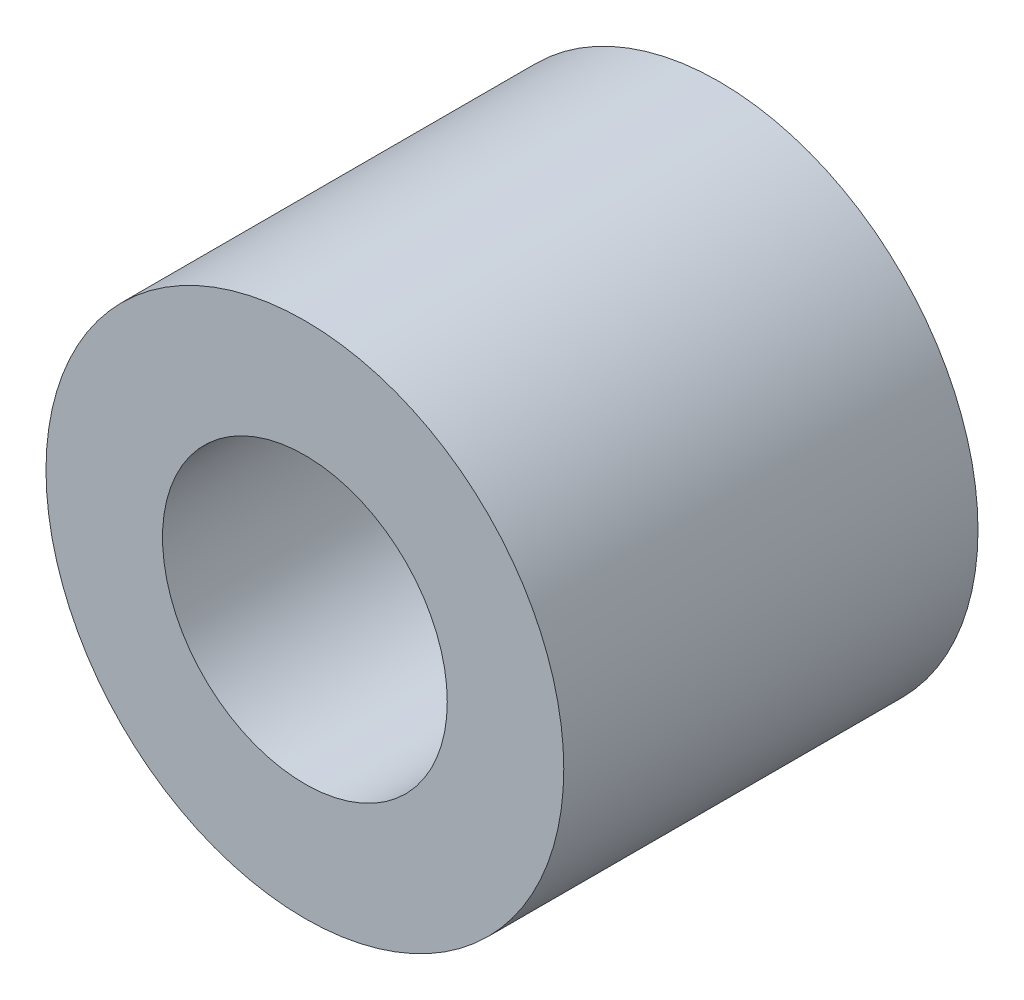
SolidWorks part; units mm, degrees
ref_plane "Plano frontal" through (0, 0, 0) normal (0, 0, 1) x (1, 0, 0)
ref_plane "Plano superior" through (0, 0, 0) normal (0, 1, 0) x (1, 0, 0)
ref_plane "Plano direito" through (0, 0, 0) normal (1, 0, 0) x (0, 0, -1)
sketch "Sketch1" plane through (0, 0, 0) normal (0, 0, 1) x (1, 0, 0)
  circle A0 centre (0, 0) radius 2.5
  circle A1 centre (0, 0) radius 1.375
  dimension "D1" = 5
  dimension "D2" = 2.75
extrude "Boss-Extrude2" add sketch "Sketch1" along normal blind 4
